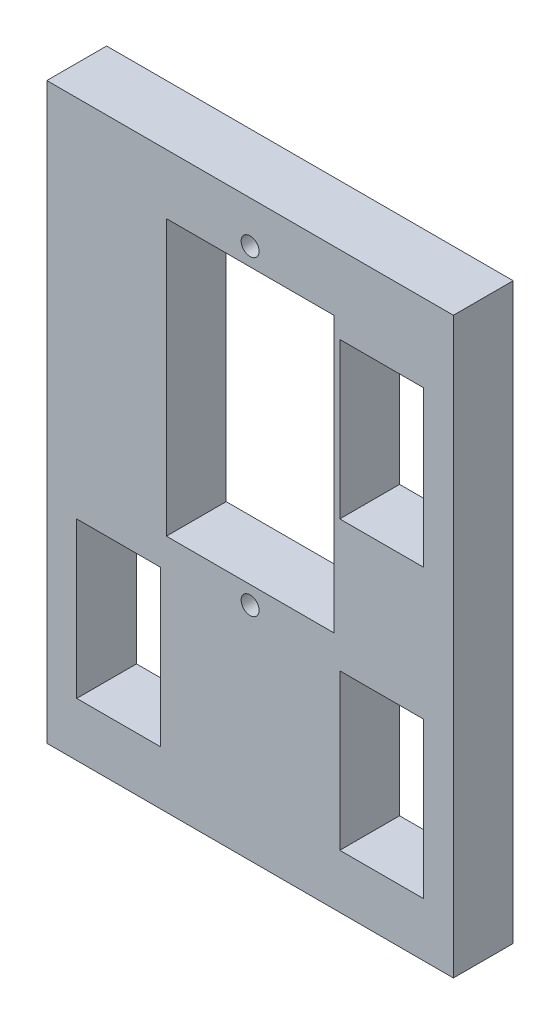
SolidWorks part; units mm, degrees
ref_plane "Alzado" through (0, 0, 0) normal (0, 0, 1) x (1, 0, 0)
ref_plane "Planta" through (0, 0, 0) normal (0, 1, 0) x (1, 0, 0)
ref_plane "Vista lateral" through (0, 0, 0) normal (1, 0, 0) x (0, 0, -1)
sketch "Croquis1" plane through (0, 0, 0) normal (0, 0, 1) x (1, 0, 0)
  line L0 (2.5, 48) -> (2.5, 0) construction
  line L1 (0, 0) -> (34, 0)
  line L2 (0, 0) -> (0, 48)
  line L3 (0, 48) -> (34, 48)
  line L4 (34, 0) -> (34, 48)
  line L5 (31.5, 48) -> (31.5, 0) construction
  line L6 (9.5, 48) -> (9.5, 0) construction
  line L7 (24.5, 48) -> (24.5, 0) construction
  line L8 (17, 48) -> (17, 0) construction
  line L10 (24, 20) -> (10, 20)
  line L11 (24, 20) -> (24, 43)
  line L12 (24, 43) -> (10, 43)
  line L13 (10, 20) -> (10, 43)
  line L14 (24, 20) -> (10, 43) construction
  line L15 (24, 43) -> (10, 20) construction
  line L16 (31.5, 4.5) -> (24.5, 4.5)
  line L17 (31.5, 4.5) -> (31.5, 17.5)
  line L18 (31.5, 17.5) -> (24.5, 17.5)
  line L19 (24.5, 4.5) -> (24.5, 17.5)
  line L20 (31.5, 28.5) -> (24.5, 28.5)
  line L21 (31.5, 28.5) -> (31.5, 41.5)
  line L22 (31.5, 41.5) -> (24.5, 41.5)
  line L23 (24.5, 28.5) -> (24.5, 41.5)
  line L24 (9.5, 4.5) -> (2.5, 4.5)
  line L25 (9.5, 4.5) -> (9.5, 17.5)
  line L26 (9.5, 17.5) -> (2.5, 17.5)
  line L27 (2.5, 4.5) -> (2.5, 17.5)
  circle A0 centre (17, 18.5) radius 0.75
  circle A1 centre (17, 44.5) radius 0.75
  point P15 (17, 31.5)
  point P36 (6, 4.5)
  dimension "D9" = 1.5
  dimension "D10" = 1.5
  dimension "D1" = 7
  dimension "D2" = 7
  dimension "D3" = 2.5
  dimension "D4" = 2.5
  dimension "D5" = 15
  dimension "D6" = 14
  dimension "D7" = 23
  dimension "D8" = 20
  dimension "D11" = 1.5
  dimension "D12" = 1.5
  dimension "D13" = 4.5
  dimension "D14" = 4.5
  dimension "D15" = 13
  dimension "D16" = 13
  dimension "D17" = 11
  dimension "D18" = 13
  dimension "D19" = 48
extrude "Saliente-Extruir1" add sketch "Croquis1" along normal blind 5
